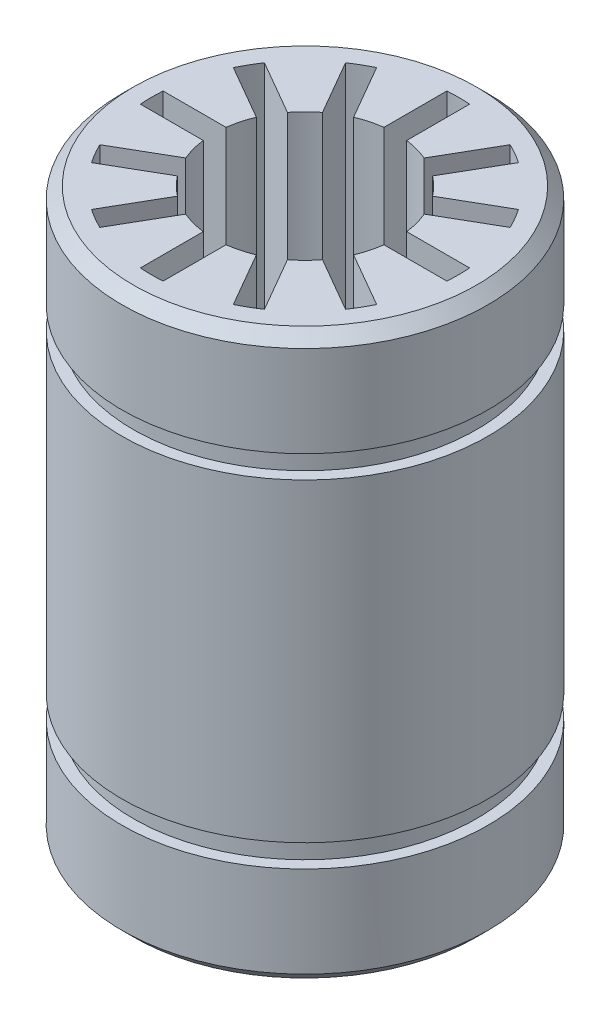
SolidWorks part; units mm, degrees
material "PTFE (général)"
ref_plane "Plan de face" through (0, 0, 0) normal (0, 0, 1) x (1, 0, 0)
ref_plane "Plan de dessus" through (0, 0, 0) normal (0, 1, 0) x (1, 0, 0)
ref_plane "Plan de droite" through (0, 0, 0) normal (1, 0, 0) x (0, 0, -1)
sketch "Esquisse2" plane through (0, 0, 0) normal (0, 0, 1) x (1, 0, 0)
  line L0 (0, 12.4) -> (-8.0383, 12.4)
  line L1 (-8.0383, 12.4) -> (-8.0383, 7.9)
  line L2 (-8.0383, 7.9) -> (-7.5383, 7.9)
  line L3 (-7.5383, 7.9) -> (-7.5383, 6.9)
  line L4 (-7.5383, 6.9) -> (-8.0383, 6.9)
  line L5 (-8.0383, 6.9) -> (-8.0383, -6.9)
  line L6 (-8.0383, -6.9) -> (-7.5383, -6.9)
  line L7 (-7.5383, -6.9) -> (-7.5383, -7.9)
  line L8 (-7.5383, -7.9) -> (-8.0383, -7.9)
  line L9 (-8.0383, -7.9) -> (-8.0383, -12.4)
  line L10 (-8.0383, -12.4) -> (0, -12.4)
  line L11 (0, 0) -> (0, -17.1141) construction
  line L12 (0, 12.4) -> (0, -12.4)
  dimension "D1" = 1
  dimension "D2" = 0.5
  dimension "D3" = 4.5
  dimension "D4" = 12.4
  dimension "D5" = 24.8
revolve "Révolution1" add sketch "Esquisse2" angle 360 about L11
chamfer "Chanfrein1" distance 0.5 angle 45 2 edges at (-8.0383, -12.4, 0) (-8.0383, 12.4, 0)
sketch "Esquisse3" plane through (0, 12.4, 0) normal (0, 1, 0) x (1, 0, 0)
  line L0 (0, 8.0383) -> (0, 0) construction
  line L1 (-0.5, 6.7315) -> (-0.5, 3.9686)
  line L2 (0.5, 6.7315) -> (0.5, 3.9686)
  line L3 (2.9327, 6.0796) -> (1.5513, 3.6869)
  line L4 (3.7987, 5.5796) -> (2.4173, 3.1869)
  line L5 (5.5796, 3.7987) -> (3.1869, 2.4173)
  line L6 (6.0796, 2.9327) -> (3.6869, 1.5513)
  line L7 (6.7315, 0.5) -> (3.9686, 0.5)
  line L8 (6.7315, -0.5) -> (3.9686, -0.5)
  line L9 (6.0796, -2.9327) -> (3.6869, -1.5513)
  line L10 (5.5796, -3.7987) -> (3.1869, -2.4173)
  line L11 (3.7987, -5.5796) -> (2.4173, -3.1869)
  line L12 (2.9327, -6.0796) -> (1.5513, -3.6869)
  line L13 (0.5, -6.7315) -> (0.5, -3.9686)
  line L14 (-0.5, -6.7315) -> (-0.5, -3.9686)
  line L15 (-2.9327, -6.0796) -> (-1.5513, -3.6869)
  line L16 (-3.7987, -5.5796) -> (-2.4173, -3.1869)
  line L17 (-5.5796, -3.7987) -> (-3.1869, -2.4173)
  line L18 (-6.0796, -2.9327) -> (-3.6869, -1.5513)
  line L19 (-6.7315, -0.5) -> (-3.9686, -0.5)
  line L20 (-6.7315, 0.5) -> (-3.9686, 0.5)
  line L21 (-6.0796, 2.9327) -> (-3.6869, 1.5513)
  line L22 (-5.5796, 3.7987) -> (-3.1869, 2.4173)
  line L23 (-3.7987, 5.5796) -> (-2.4173, 3.1869)
  line L24 (-2.9327, 6.0796) -> (-1.5513, 3.6869)
  circle A0 centre (0, 0) radius 6.75 construction
  circle A1 centre (0, 0) radius 4 construction
  circle A2 centre (0, 0) radius 8.0383 construction
  arc A3 (0.5, 6.7315) -> (-0.5, 6.7315) centre (0, 0) ccw
  arc A4 (-0.5, 3.9686) -> (-1.5513, 3.6869) centre (0, 0) ccw
  arc A5 (3.7987, 5.5796) -> (2.9327, 6.0796) centre (0, 0) ccw
  arc A6 (6.0796, 2.9327) -> (5.5796, 3.7987) centre (0, 0) ccw
  arc A7 (6.7315, -0.5) -> (6.7315, 0.5) centre (0, 0) ccw
  arc A8 (5.5796, -3.7987) -> (6.0796, -2.9327) centre (0, 0) ccw
  arc A9 (2.9327, -6.0796) -> (3.7987, -5.5796) centre (0, 0) ccw
  arc A10 (-0.5, -6.7315) -> (0.5, -6.7315) centre (0, 0) ccw
  arc A11 (-3.7987, -5.5796) -> (-2.9327, -6.0796) centre (0, 0) ccw
  arc A12 (-6.0796, -2.9327) -> (-5.5796, -3.7987) centre (0, 0) ccw
  arc A13 (-6.7315, 0.5) -> (-6.7315, -0.5) centre (0, 0) ccw
  arc A14 (-5.5796, 3.7987) -> (-6.0796, 2.9327) centre (0, 0) ccw
  arc A15 (-2.9327, 6.0796) -> (-3.7987, 5.5796) centre (0, 0) ccw
  arc A16 (1.5513, 3.6869) -> (0.5, 3.9686) centre (0, 0) ccw
  arc A17 (3.1869, 2.4173) -> (2.4173, 3.1869) centre (0, 0) ccw
  arc A18 (3.9686, 0.5) -> (3.6869, 1.5513) centre (0, 0) ccw
  arc A19 (3.6869, -1.5513) -> (3.9686, -0.5) centre (0, 0) ccw
  arc A20 (2.4173, -3.1869) -> (3.1869, -2.4173) centre (0, 0) ccw
  arc A21 (0.5, -3.9686) -> (1.5513, -3.6869) centre (0, 0) ccw
  arc A22 (-1.5513, -3.6869) -> (-0.5, -3.9686) centre (0, 0) ccw
  arc A23 (-3.1869, -2.4173) -> (-2.4173, -3.1869) centre (0, 0) ccw
  arc A24 (-3.9686, -0.5) -> (-3.6869, -1.5513) centre (0, 0) ccw
  arc A25 (-3.6869, 1.5513) -> (-3.9686, 0.5) centre (0, 0) ccw
  arc A26 (-2.4173, 3.1869) -> (-3.1869, 2.4173) centre (0, 0) ccw
  point P57 (0, 0)
  dimension "D1" = 13.5
  dimension "D2" = 4
  dimension "D5" = 8
  dimension "D3" = 1
  dimension "D4" = 0.5
  dimension "D6" = 12
extrude "Enlèv. mat.-Extru.1" cut sketch "Esquisse3" against normal through all
